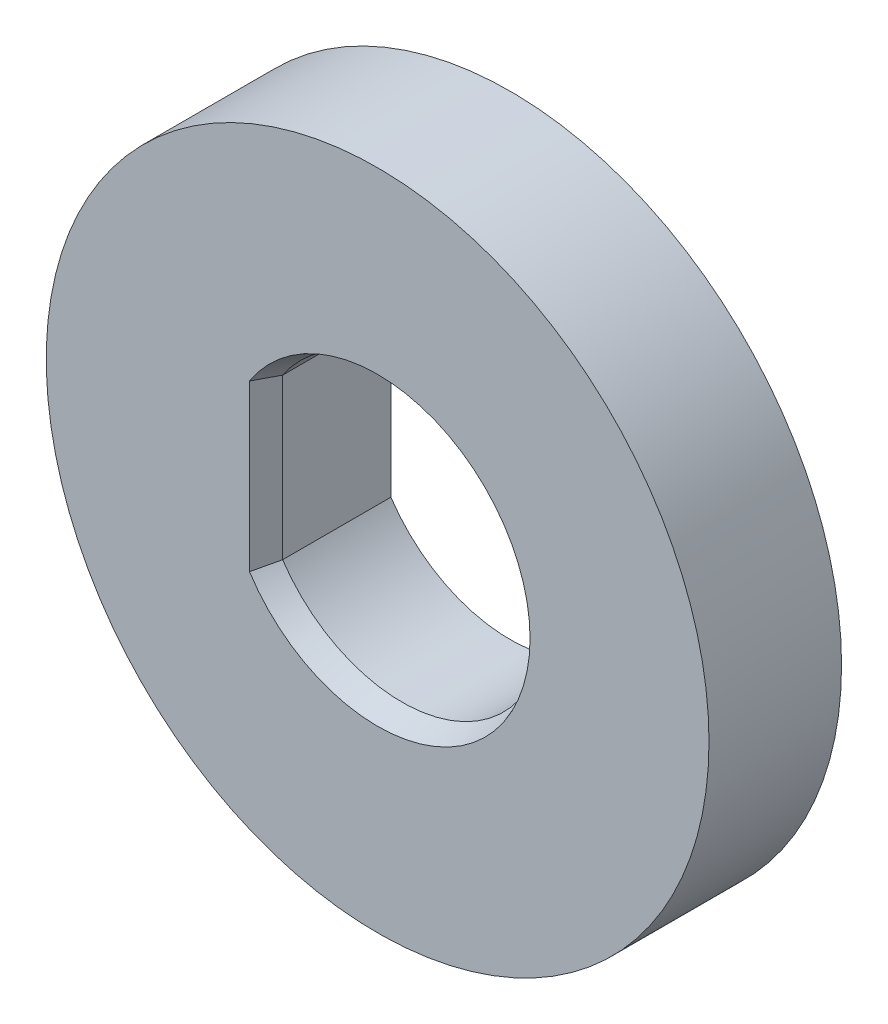
SolidWorks part; units mm, degrees
ref_plane "Front Plane" through (0, 0, 0) normal (0, 0, 1) x (1, 0, 0)
ref_plane "Top Plane" through (0, 0, 0) normal (0, 1, 0) x (1, 0, 0)
ref_plane "Right Plane" through (0, 0, 0) normal (1, 0, 0) x (0, 0, -1)
sketch "Sketch1" plane through (0, 0, 0) normal (0, 0, 1) x (1, 0, 0)
  line L0 (-2.7, 1.809) -> (-2.7, -1.809)
  circle A0 centre (0, 0) radius 7.5
  circle A1 centre (0, 0) radius 3.25
  dimension "D1" = 15
  dimension "D2" = 6.5
  dimension "D3" = 2.7
extrude "Boss-Extrude1" add sketch "Sketch1" along normal blind 3 contours A0 A1 | L0 A1
chamfer "Chamfer3" distance 0.2 angle 70 2 edges at (-2.7, 0, 3) (3.25, 0, 3)
